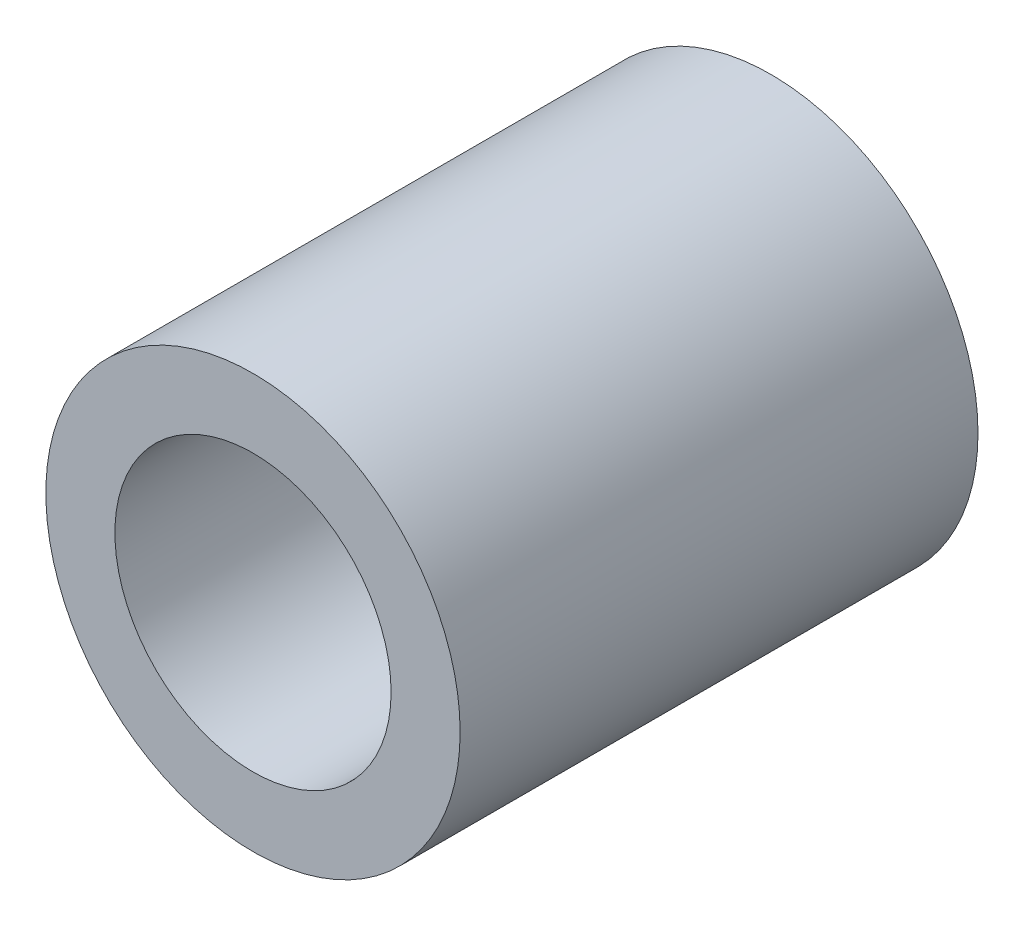
SolidWorks part; units mm, degrees
ref_plane "Front Plane" through (0, 0, 0) normal (0, 0, 1) x (1, 0, 0)
ref_plane "Top Plane" through (0, 0, 0) normal (0, 1, 0) x (1, 0, 0)
ref_plane "Right Plane" through (0, 0, 0) normal (1, 0, 0) x (0, 0, -1)
sketch "Sketch1" plane through (0, 0, 0) normal (0, 0, 1) x (1, 0, 0)
  circle A0 centre (0, 0) radius 12
  circle A1 centre (0, 0) radius 8
  dimension "D1" = 24
  dimension "D2" = 16
extrude "Boss-Extrude1" add sketch "Sketch1" along normal blind 30
